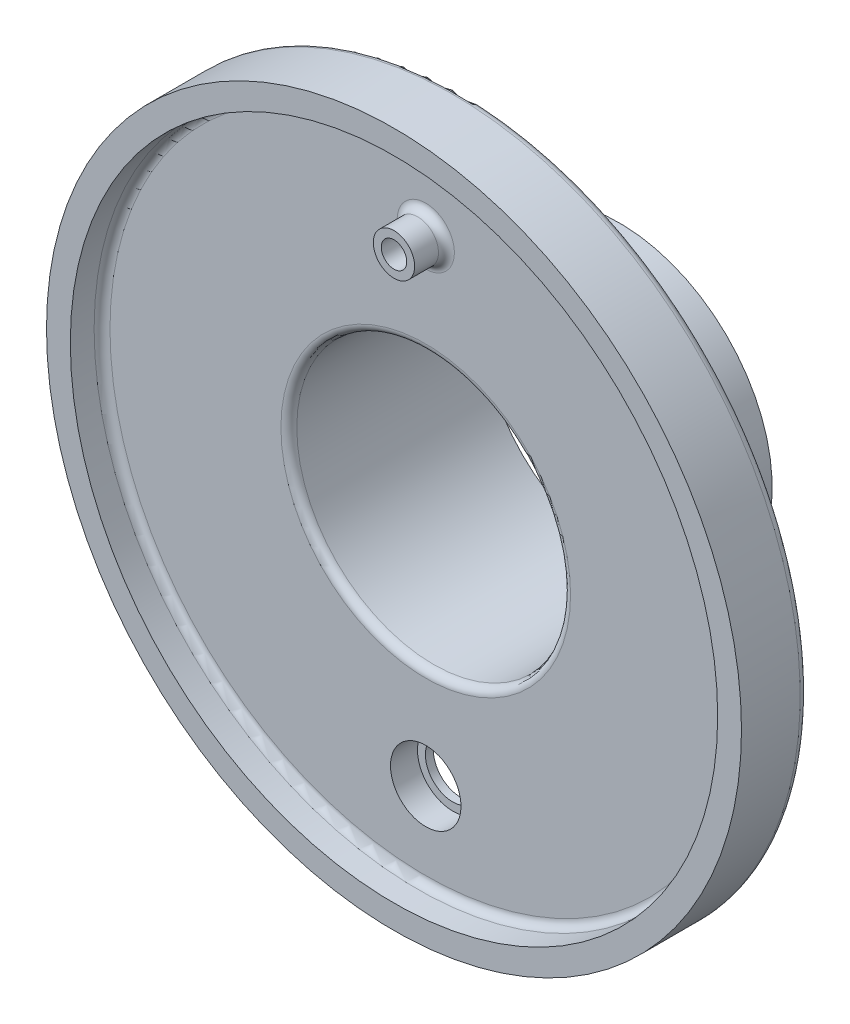
SolidWorks part; units mm, degrees
ref_plane "Front Plane" through (0, 0, 0) normal (0, 0, 1) x (1, 0, 0)
ref_plane "Top Plane" through (0, 0, 0) normal (0, 1, 0) x (1, 0, 0)
ref_plane "Right Plane" through (0, 0, 0) normal (1, 0, 0) x (0, 0, -1)
sketch "Sketch1" plane through (0, 0, 0) normal (0, 0, 1) x (1, 0, 0)
  circle A0 centre (0, 0) radius 103.5939
  circle A1 centre (0, 0) radius 111.2139
  dimension "D1" = 207.1878
  dimension "D2" = 7.62
extrude "Boss-Extrude1" add sketch "Sketch1" along normal blind 10.16
sketch "Sketch2" plane through (0, 0, 0) normal (0, 0, -1) x (-1, 0, 0)
  circle A0 centre (0, 0) radius 111.2139
  circle A1 centre (0, 0) radius 43.815
  circle A2 centre (0, 0) radius 111.2139 construction
  dimension "D1" = 87.63
extrude "Boss-Extrude3" add sketch "Sketch2" along normal blind 11.176
sketch "Sketch3" plane through (0, 0, -11.176) normal (0, 0, -1) x (-1, 0, 0)
  circle A0 centre (0, 0) radius 48.895
  circle A1 centre (0, 0) radius 43.815
  circle A2 centre (0, 0) radius 43.815 construction
  dimension "D1" = 5.08
extrude "Boss-Extrude4" add sketch "Sketch3" along normal blind 50.8
fillet "Fillet1" radius 2.54 1 edges at (103.5939, 0, 0)
fillet "Fillet2" radius 2.54 3 edges at (-48.895, 0, -11.176) (-111.2139, 0, -11.176) (-43.815, 0, 0)
sketch "Sketch4" plane through (0, 0, -11.176) normal (0, 0, -1) x (-1, 0, 0)
  circle A0 centre (0, 0) radius 76.2
  circle A1 centre (0, -76.2) radius 11.2776
  dimension "D1" = 152.4
  dimension "D2" = 22.5552
extrude "Cut-Extrude1" cut sketch "Sketch4" against normal blind 50.8 contours A0 A1 | A0 A1
sketch "Sketch5" plane through (0, 0, 0) normal (0, 0, 1) x (1, 0, 0)
  circle A0 centre (0, 0) radius 76.2
  circle A1 centre (0, 76.2) radius 4.0767
  circle A2 centre (0, 76.2) radius 6.6167
  dimension "D1" = 152.4
  dimension "D2" = 2.54
  dimension "D3" = 8.1534
extrude "Boss-Extrude5" add sketch "Sketch5" along normal blind 10.16 contours A0 A2 A1 | A0 A2 A1
fillet "Fillet3" radius 2.54 1 edges at (-6.6167, 76.2, 0)
sketch "Sketch6" plane through (0, 0, -11.176) normal (0, 0, -1) x (-1, 0, 0)
  circle A0 centre (0, -76.2) radius 11.2776
  circle A1 centre (0, -76.2) radius 11.2776 construction
  circle A2 centre (0, -76.2) radius 8.7376
  dimension "D1" = 2.54
extrude "Boss-Extrude6" add sketch "Sketch6" against normal blind 2.54
